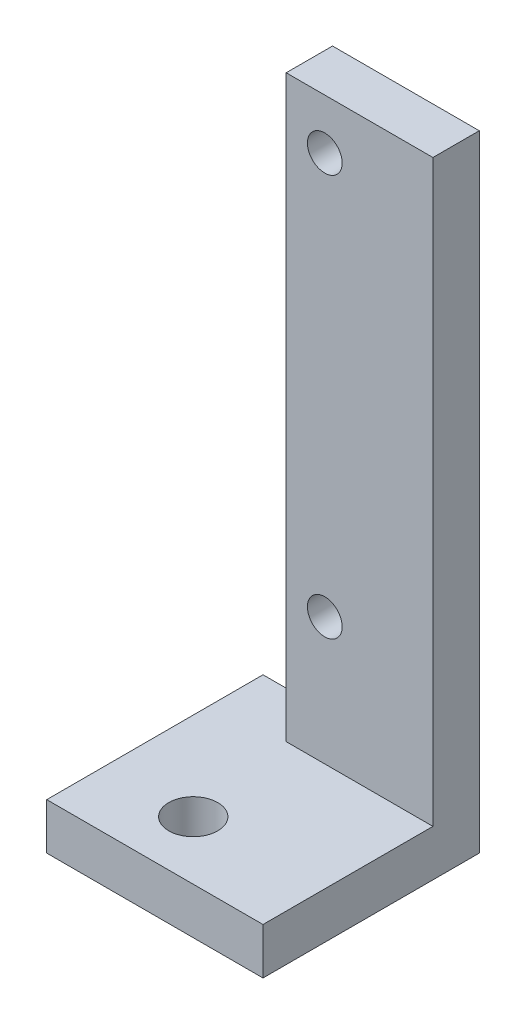
SolidWorks part; units mm, degrees
ref_plane "Front Plane" through (0, 0, 0) normal (0, 0, 1) x (1, 0, 0)
ref_plane "Top Plane" through (0, 0, 0) normal (0, 1, 0) x (1, 0, 0)
ref_plane "Right Plane" through (0, 0, 0) normal (1, 0, 0) x (0, 0, -1)
sketch "Sketch1" plane through (0, 0, 0) normal (0, 0, 1) x (1, 0, 0)
  line L0 (55, 0) -> (-55, 0) construction
  line L1 (-5, 32.5) -> (5, 32.5)
  line L2 (-5, 32.5) -> (-5, -32.5)
  line L3 (-5, -32.5) -> (5, -32.5)
  line L4 (5, 32.5) -> (5, -32.5)
  line L5 (-5, 32.5) -> (5, -32.5) construction
  line L6 (-5, -32.5) -> (5, 32.5) construction
  line L8 (-5, -32.5) -> (5, -32.5)
  line L9 (-5, -32.5) -> (-5, -42.5)
  line L10 (-5, -42.5) -> (5, -42.5)
  line L11 (5, -32.5) -> (5, -42.5)
  circle A0 centre (0, 26) radius 2.25
  circle A1 centre (0, -26) radius 2.25
  point P0 (0, 0)
  dimension "D2" = 4.5
  dimension "D1" = 65
  dimension "D3" = 26
  dimension "D4" = 10
  dimension "D5" = 10
extrude "Boss-Extrude1" add sketch "Sketch1" along normal blind 6 contours L11 L3 L9 L10 | L4 L1 L2 L3 A0 A1
sketch "Sketch2" plane through (0, -42.5, 0) normal (0, -1, 0) x (1, 0, 0)
  line L0 (-14, 0) -> (-14, 28)
  line L1 (-14, 0) -> (14, 0)
  line L2 (0, 0) -> (0, 28)
  line L3 (-14, 28) -> (14, 28)
  line L4 (14, 0) -> (14, 28)
  circle A0 centre (2.6, 20.4299) radius 3.175
  line M2 (-5, 0) -> (5, 0)
  line M3 (5, 0) -> (5, 6)
  line M4 (5, 6) -> (-5, 6)
  line M5 (-5, 6) -> (-5, 0)
  dimension "D2" = 6.35
  dimension "D1" = 2.6
  dimension "D3" = 28
  dimension "D4" = 28
extrude "Boss-Extrude2" add sketch "Sketch2" along normal blind 6 separate body contours L3 L0 L1 L2 M5 M4 | L2 M2 M4 M5 | L2 L1 M3 M4 | L1 L4 L3 L2 A0 M4 M3
sketch "Sketch3" plane through (-5, 0, 0) normal (-1, 0, 0) x (0, 0, 1)
  line L0 (0, -42.5) -> (28, -42.5) construction
  line L1 (0, 32.5) -> (6, 32.5)
  line L2 (0, 32.5) -> (0, -42.5)
  line L3 (0, -42.5) -> (6, -42.5)
  line L4 (6, 32.5) -> (6, -42.5)
extrude "Boss-Extrude3" add sketch "Sketch3" along normal up to surface (9 mm away) up to face at (-14, -45.5, 14)
mirror "Mirror1" about plane through (-14, -48.5, 0) normal (-1, 0, 0) of bodies 103
sketch "Sketch4" plane through (0, 0, 6) normal (0, 0, 1) x (1, 0, 0)
  line L0 (-33, 32.5) -> (5, 32.5) construction
  line L1 (-14, 32.5) -> (40.2051, 32.5)
  line L2 (-14, 32.5) -> (-14, -71.1316)
  line L3 (-14, -71.1316) -> (40.2051, -71.1316)
  line L4 (40.2051, 32.5) -> (40.2051, -71.1316)
extrude "Cut-Extrude1" cut sketch "Sketch4" against normal through all both and the other way through all
